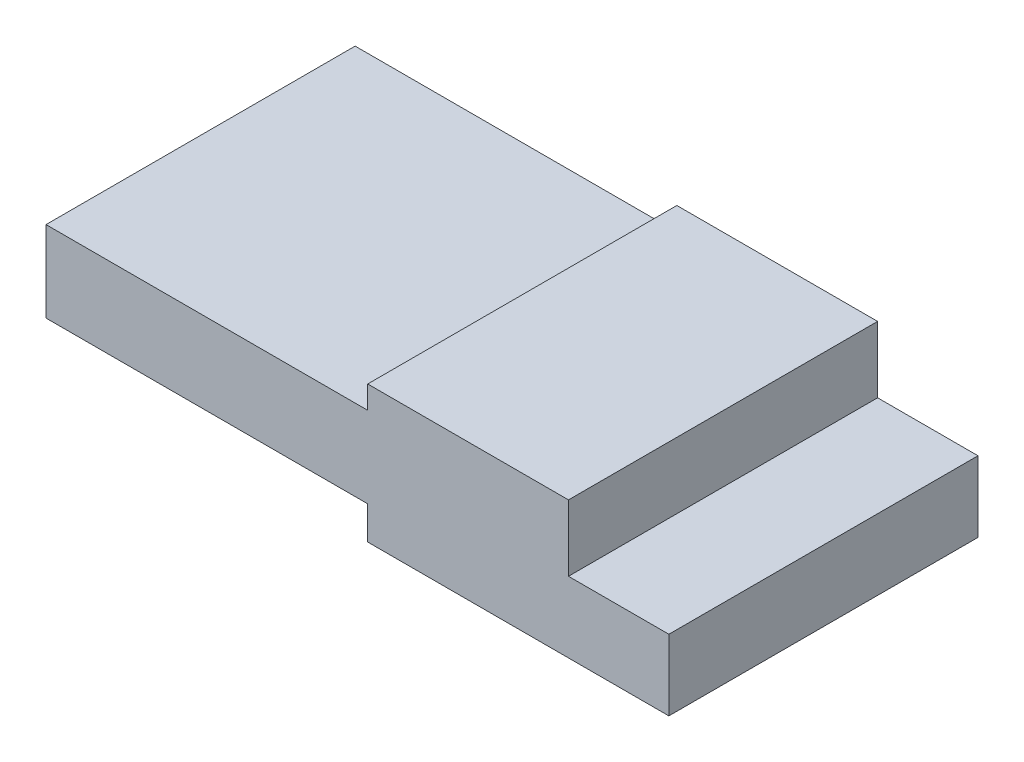
SolidWorks part; units mm, degrees
ref_plane "Front Plane" through (0, 0, 0) normal (0, 0, 1) x (1, 0, 0)
ref_plane "Top Plane" through (0, 0, 0) normal (0, 1, 0) x (1, 0, 0)
ref_plane "Right Plane" through (0, 0, 0) normal (1, 0, 0) x (0, 0, -1)
sketch "Sketch1" plane through (0, 0, 0) normal (0, 0, 1) x (1, 0, 0)
  line L0 (0, 0) -> (0, 1.8034)
  line L1 (0, 1.8034) -> (7.1628, 1.8034)
  line L2 (7.1628, 1.8034) -> (7.1628, 2.3114)
  line L3 (7.1628, 2.3114) -> (11.6332, 2.3114)
  line L4 (11.6332, 2.3114) -> (11.6332, 0.8382)
  line L5 (11.6332, 0.8382) -> (13.8684, 0.8382)
  line L6 (13.8684, 0.8382) -> (13.8684, -0.7366)
  line L7 (13.8684, -0.7366) -> (7.1628, -0.7366)
  line L8 (7.1628, -0.7366) -> (7.1628, 0)
  line L9 (7.1628, 0) -> (0, 0)
  dimension "D1" = 1.8034
  dimension "D2" = 7.1628
  dimension "D3" = 11.6332
  dimension "D4" = 13.8684
  dimension "D5" = 0.508
  dimension "D6" = 3.048
  dimension "D7" = 1.5748
extrude "Boss-Extrude1" add sketch "Sketch1" along normal blind 6.8834
ref_plane "Plane1" through (4.1656, 0, 0) normal (-1, 0, 0) x (0, 0, 1)
